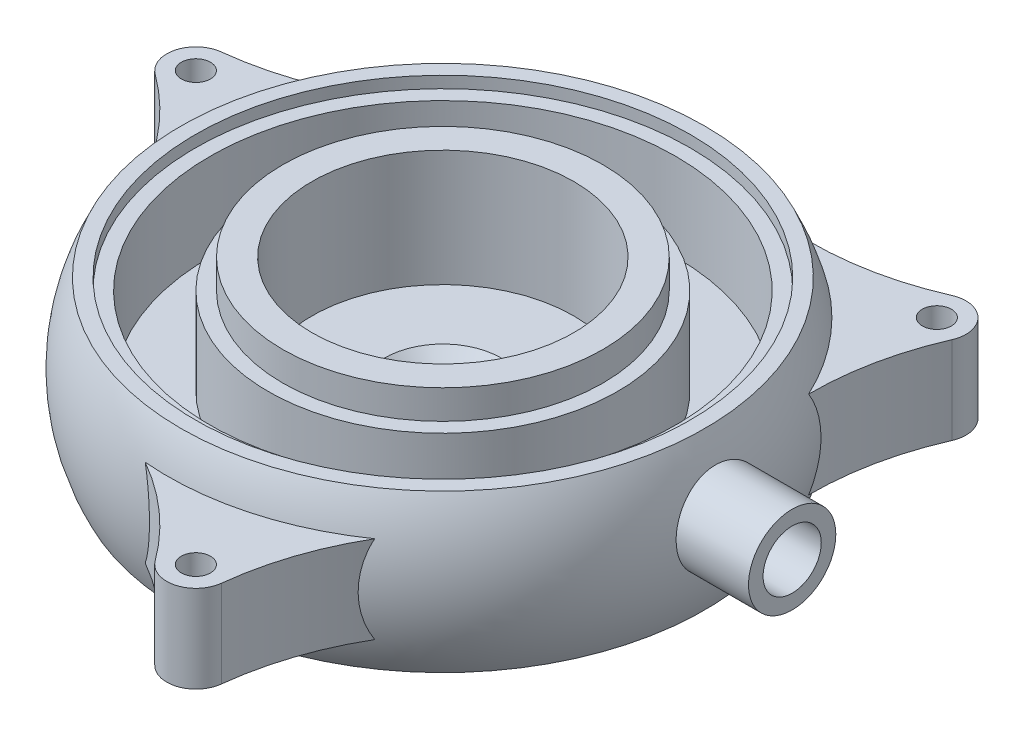
SolidWorks part; units mm, degrees
material "AISI 1020"
ref_plane "Front Plane" through (0, 0, 0) normal (0, 0, 1) x (1, 0, 0)
ref_plane "Top Plane" through (0, 0, 0) normal (0, 1, 0) x (1, 0, 0)
ref_plane "Right Plane" through (0, 0, 0) normal (1, 0, 0) x (0, 0, -1)
sketch "Sketch1" plane through (0, 0, 0) normal (0, 0, 1) x (1, 0, 0)
  line L0 (0, 0) -> (0, 65.0339) construction
  line L1 (10, 0) -> (20, 10)
  line L2 (20, 10) -> (45, 10)
  line L3 (45, 10) -> (45, 50)
  line L4 (45, 50) -> (55, 50)
  line L5 (55, 50) -> (55, 40)
  line L6 (55, 40) -> (60, 40)
  line L7 (60, 40) -> (60, 10)
  line L8 (60, 10) -> (80, 10)
  line L9 (80, 10) -> (80, 40)
  line L13 (85, -10) -> (85, 0)
  line L14 (85, 0) -> (10, 0)
  line L15 (80, 40) -> (85, 40)
  line L16 (85, 40) -> (85, 44)
  line L17 (85, 44) -> (90, 44)
  line L18 (85, -10) -> (90, -10)
  arc A0 (90, 44) -> (90, -10) centre (36.4183, 17) cw
  point P19 (50, 50)
  dimension "D1" = 20
  dimension "D9" = 60
  dimension "D2" = 45
  dimension "D3" = 90
  dimension "D4" = 110
  dimension "D5" = 120
  dimension "D6" = 160
  dimension "D7" = 170
  dimension "D8" = 180
  dimension "D10" = 50
  dimension "D11" = 6
  dimension "D12" = 40
  dimension "D13" = 10
  dimension "D14" = 60
revolve "Revolve1" add sketch "Sketch1" angle 360 about L0
ref_plane "Plane1" through (0, 17, 0) normal (0, 1, 0) x (1, 0, 0)
sketch "Sketch2" plane through (0, 17, 0) normal (0, 1, 0) x (1, 0, 0)
  line L2 (0, 0) -> (0, 145.8775) construction
  line L3 (0, 0) -> (133.6368, 133.6368) construction
  circle A0 centre (0, 0) radius 90 construction
  arc A4 (80.8371, 94.0111) -> (94.0111, 80.8371) centre (84.8528, 84.8528) cw
  arc A9 (87.9129, 19.2696) -> (19.2696, 87.9129) centre (0, 0) ccw
  arc A10 (87.9129, 19.2696) -> (94.0111, 80.8371) centre (185.594, 40.6802) cw
  arc A11 (19.2696, 87.9129) -> (80.8371, 94.0111) centre (40.6802, 185.594) ccw
  circle A12 centre (84.8528, 84.8528) radius 5
  dimension "D2" = 120
  dimension "D4" = 10
  dimension "D5" = 100
  dimension "D3" = 10
  dimension "D1" = 45
extrude "Boss-Extrude2" add sketch "Sketch2" against normal mid plane 30
pattern_circular "CirPattern1" count 3 over 360 about axis through (0, 0, 0) along (0, 1, 0) of "Boss-Extrude2"
ref_plane "Plane2" through (120, 0, 0) normal (1, 0, 0) x (0, 0, -1)
sketch "Sketch4" plane through (120, 0, 0) normal (1, 0, 0) x (0, 0, -1)
  line L0 (-90, -10) -> (90, -10) construction
  circle A0 centre (0, 20) radius 15
  dimension "D2" = 30
  dimension "D1" = 30
extrude "Boss-Extrude3" add sketch "Sketch4" against normal up to next
sketch "Sketch5" plane through (120, 0, 0) normal (1, 0, 0) x (0, 0, -1)
  circle A0 centre (0, 20) radius 10
  dimension "D1" = 20
extrude "Cut-Extrude1" cut sketch "Sketch5" against normal up to surface (40.6275 mm away)
